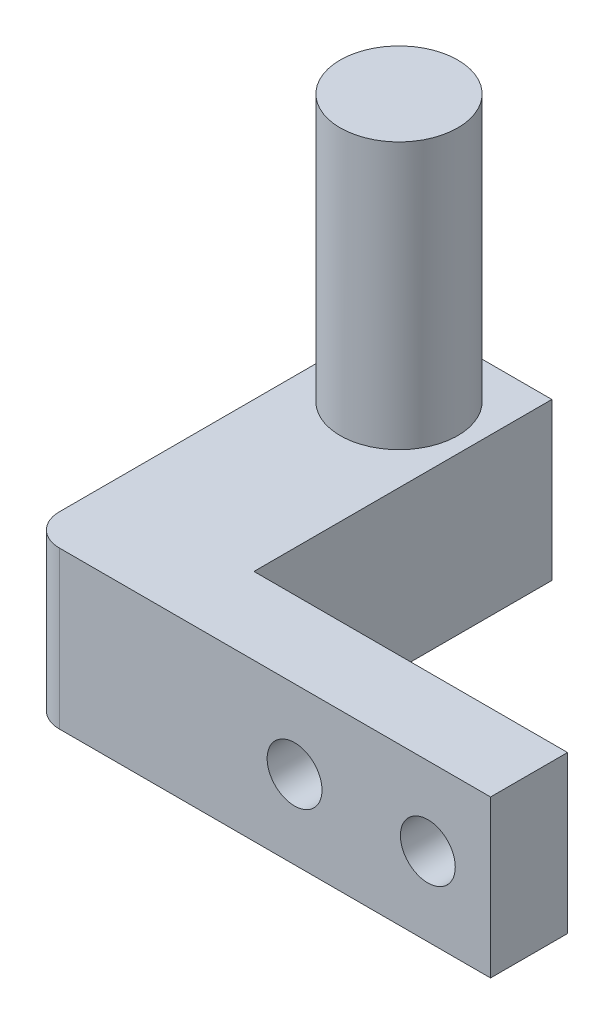
SolidWorks part; units mm, degrees
ref_plane "Front Plane" through (0, 0, 0) normal (0, 0, 1) x (1, 0, 0)
ref_plane "Top Plane" through (0, 0, 0) normal (0, 1, 0) x (1, 0, 0)
ref_plane "Right Plane" through (0, 0, 0) normal (1, 0, 0) x (0, 0, -1)
sketch "Sketch1" plane through (0, 0, 0) normal (0, 0, 1) x (1, 0, 0)
  line L1 (0, 0) -> (12.5, 0)
  line L2 (0, 0) -> (0, 10)
  line L3 (0, 10) -> (12.5, 10)
  line L4 (12.5, 0) -> (12.5, 10)
  dimension "D1" = 12.5
  dimension "D2" = 10
extrude "Boss-Extrude1" add sketch "Sketch1" along normal blind 10
sketch "Sketch2" plane through (0, 0, 0) normal (-1, 0, 0) x (0, 0, 1)
  line L0 (10, 0) -> (0, 0) construction
  line L1 (10, 0) -> (0, 0)
  line L2 (10, 0) -> (10, 10)
  line L3 (10, 10) -> (0, 10)
  line L4 (0, 0) -> (0, 10)
  line L5 (0, 10) -> (0, 0) construction
extrude "Boss-Extrude2" add sketch "Sketch2" along normal blind 5
sketch "Sketch3" plane through (0, 10, 0) normal (0, 1, 0) x (1, 0, 0)
  line L0 (12.5, -10) -> (12.5, 0) construction
  line L1 (12.5, 0) -> (-5, 0) construction
  circle A0 centre (3.75, -5) radius 3.75
  point P5 (12.5, -5)
  point P9 (3.75, 0)
  dimension "D1" = 7.5
extrude "Boss-Extrude3" add sketch "Sketch3" along normal blind 17
sketch "Sketch4" plane through (0, 10, 0) normal (0, 1, 0) x (1, 0, 0)
  line L0 (12.5, 0) -> (-5, 0) construction
  line L1 (12.5, 0) -> (8.5, 0)
  line L2 (12.5, 0) -> (12.5, -10)
  line L3 (12.5, -10) -> (8.5, -10)
  line L4 (8.5, 0) -> (8.5, -10)
  line L5 (12.5, -10) -> (-5, -10) construction
  line L6 (12.5, -10) -> (12.5, 0) construction
  line L7 (3.75, 0) -> (3.75, -3.716) construction
  line L8 (-5, -10) -> (-1, -10)
  line L9 (-5, 0) -> (-5, -10)
  line L10 (-5, 0) -> (-1, 0)
  line L11 (-1, 0) -> (-1, -10)
  dimension "D1" = 4
extrude "Cut-Extrude1" cut sketch "Sketch4" against normal through all
sketch "Sketch5" plane through (0, 0, 10) normal (0, 0, 1) x (1, 0, 0)
  line L0 (-1, 0) -> (8.5, 0) construction
  line L1 (8.5, 0) -> (-1, 0)
  line L2 (8.5, 0) -> (8.5, 10)
  line L3 (8.5, 10) -> (-1, 10)
  line L4 (-1, 0) -> (-1, 10)
  line L5 (-1, 0) -> (-1, 10) construction
  line L6 (8.5, 10) -> (-1, 10) construction
  line L7 (8.5, 0) -> (8.5, 10) construction
extrude "Boss-Extrude4" add sketch "Sketch5" along normal blind 12.5
sketch "Sketch6" plane through (8.5, 0, 0) normal (1, 0, 0) x (0, 0, -1)
  line L0 (0, 10) -> (-22.5, 10) construction
  line L1 (-22.5, 0) -> (-17.5, 0)
  line L2 (-22.5, 0) -> (-22.5, 10)
  line L3 (-22.5, 10) -> (-17.5, 10)
  line L4 (-17.5, 0) -> (-17.5, 10)
  line L5 (-22.5, 0) -> (-22.5, 10) construction
  line L6 (0, 0) -> (-22.5, 0) construction
  dimension "D1" = 5
extrude "Boss-Extrude5" add sketch "Sketch6" along normal blind 30
sketch "Sketch7" plane through (0, 0, 22.5) normal (0, 0, 1) x (1, 0, 0)
  line L0 (38.5, 10) -> (38.5, 0) construction
  circle A0 centre (22.5, 5) radius 1.75
  circle A1 centre (33.5, 5) radius 1.75
  point P6 (38.5, 5)
  dimension "D1" = 3.5
  dimension "D2" = 3.5
  dimension "D3" = 5
  dimension "D4" = 11
extrude "Cut-Extrude2" cut sketch "Sketch7" against normal through all
sketch "Sketch8" plane through (0, 10, 0) normal (0, 1, 0) x (1, 0, 0)
  line L0 (38.5, -22.5) -> (-1, -22.5) construction
  line L1 (38.5, -17.5) -> (8.5, -17.5)
  line L2 (38.5, -17.5) -> (38.5, -22.5)
  line L3 (38.5, -22.5) -> (8.5, -22.5)
  line L4 (8.5, -17.5) -> (8.5, -22.5)
  line L5 (8.5, 0) -> (8.5, -17.5) construction
extrude "Cut-Extrude4" cut sketch "Sketch8" against normal blind 10
sketch "Sketch10" plane through (0, 0, 22.5) normal (0, 0, 1) x (1, 0, 0)
  line L0 (8.5, 0) -> (8.5, 10) construction
  line L1 (8.5, 10) -> (-1, 10)
  line L2 (8.5, 10) -> (8.5, 0)
  line L3 (8.5, 0) -> (-1, 0)
  line L4 (-1, 10) -> (-1, 0)
  line L5 (-1, 0) -> (8.5, 0) construction
  line L6 (-1, 10) -> (-1, 0) construction
  line L7 (8.5, 10) -> (-1, 10) construction
extrude "Cut-Extrude6" cut sketch "Sketch10" against normal blind 3.49
sketch "Sketch11" plane through (0, 0, 19.01) normal (0, 0, 1) x (1, 0, 0)
  line L0 (8.5, 0) -> (8.5, 10) construction
  line L1 (8.5, 10) -> (-1, 10)
  line L2 (8.5, 10) -> (8.5, 0)
  line L3 (8.5, 0) -> (-1, 0)
  line L4 (-1, 10) -> (-1, 0)
  line L5 (-1, 10) -> (-1, 0) construction
  line L6 (8.5, 10) -> (-1, 10) construction
  line L7 (-1, 0) -> (8.5, 0) construction
extrude "Boss-Extrude6" add sketch "Sketch11" along normal blind 3.9
sketch "Sketch12" plane through (8.5, 0, 0) normal (1, 0, 0) x (0, 0, -1)
  line L0 (-22.91, 0) -> (-22.91, 10) construction
  line L1 (-22.91, 10) -> (-18.91, 10)
  line L2 (-22.91, 10) -> (-22.91, 0)
  line L3 (-22.91, 0) -> (-18.91, 0)
  line L4 (-18.91, 10) -> (-18.91, 0)
  line L5 (0, 10) -> (-22.91, 10) construction
  line L6 (0, 0) -> (-22.91, 0) construction
  dimension "D1" = 4
extrude "Boss-Extrude7" add sketch "Sketch12" along normal blind 20
sketch "Sketch13" plane through (0, 0, 0) normal (0, -1, 0) x (-1, 0, 0)
  line L0 (-28.5, -18.91) -> (-8.5, -18.91) construction
  line L1 (-8.5, -18.91) -> (-28.5, -18.91)
  line L2 (-8.5, -18.91) -> (-8.5, -19)
  line L3 (-8.5, -19) -> (-28.5, -19)
  line L4 (-28.5, -18.91) -> (-28.5, -19)
  line L5 (-28.5, -22.91) -> (-28.5, -18.91) construction
  line L6 (-8.5, 0) -> (-8.5, -18.91) construction
  dimension "D1" = 0.09
extrude "Cut-Extrude7" cut sketch "Sketch13" against normal through all
sketch "Sketch14" plane through (0, 0, 22.91) normal (0, 0, 1) x (1, 0, 0)
  line L0 (-1, 10) -> (-1, 0) construction
  line L1 (-1, 0) -> (28.5, 0) construction
  line L2 (28.5, 10) -> (28.5, 0) construction
  circle A0 centre (16, 5) radius 1.75
  circle A1 centre (24.5, 5) radius 1.75
  dimension "D1" = 3.5
  dimension "D4" = 3.5
  dimension "D2" = 17
  dimension "D3" = 5
  dimension "D5" = 4
extrude "Cut-Extrude8" cut sketch "Sketch14" against normal through all
sketch "Sketch15" plane through (0, 0, 22.91) normal (0, 0, 1) x (1, 0, 0)
  line L0 (-1, 10) -> (-1, 0) construction
  line L1 (-1, 10) -> (28.5, 10)
  line L2 (-1, 10) -> (-1, 0)
  line L3 (-1, 0) -> (28.5, 0)
  line L4 (28.5, 10) -> (28.5, 0)
  line L5 (28.5, 10) -> (-1, 10) construction
  line L6 (28.5, 10) -> (28.5, 0) construction
  line L7 (-1, 0) -> (28.5, 0) construction
  circle A0 centre (24.5, 5) radius 1.75
  circle A1 centre (16, 5) radius 1.75
  circle A2 centre (24.5, 5) radius 1.75 construction
  circle A3 centre (16, 5) radius 1.75 construction
extrude "Boss-Extrude8" add sketch "Sketch15" along normal blind 1
fillet "Fillet1" radius 2 1 edges at (-1, 5, 23.91)
